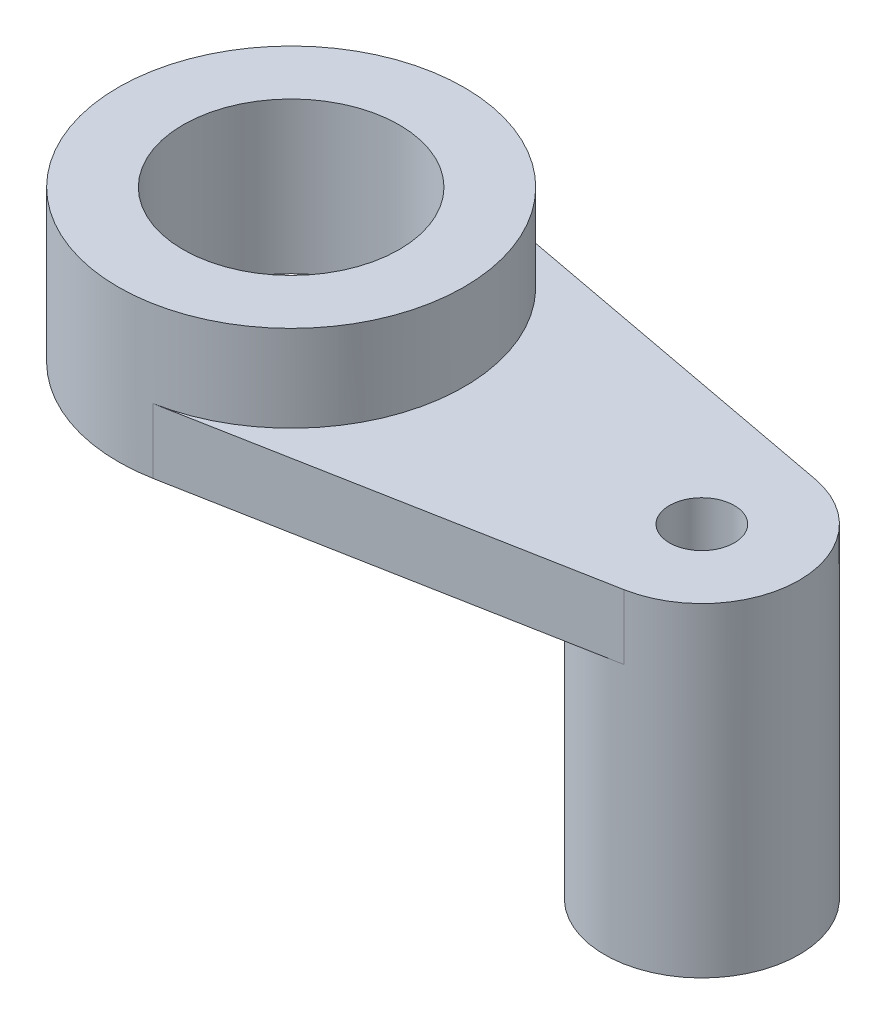
SolidWorks part; units mm, degrees
material "Galvanized Steel"
ref_plane "Front Plane" through (0, 0, 0) normal (0, 0, 1) x (1, 0, 0)
ref_plane "Top Plane" through (0, 0, 0) normal (0, 1, 0) x (1, 0, 0)
ref_plane "Right Plane" through (0, 0, 0) normal (1, 0, 0) x (0, 0, -1)
sketch "Sketch1" plane through (0, 0, 0) normal (0, 1, 0) x (1, 0, 0)
  line L0 (0, 0) -> (30821.0122, 0) construction
  line L1 (0, 0) -> (0, 30821.0122) construction
  line L2 (42.5, 0) -> (42.5, 50000) construction
  circle A0 centre (0, 0) radius 10
  circle A1 centre (0, 0) radius 16
  dimension "D1" = 20
  dimension "D2" = 6
extrude "Boss-Extrude1" add sketch "Sketch1" along normal blind 14
sketch "Sketch2" plane through (0, 0, 0) normal (0, 1, 0) x (1, 0, 0)
  line L0 (38, 0) -> (38, 50000) construction
  line L1 (47, 0.7036) -> (47, 50000.7036) construction
  line L2 (0, 0) -> (50000, 0) construction
  line L3 (2.9474, 15.7262) -> (39.6579, 8.846)
  line L4 (2.9474, -15.7262) -> (39.6579, -8.846)
  arc A1 (39.6579, -8.846) -> (39.6579, 8.846) centre (38, 0) ccw
  arc A2 (2.9474, -15.7262) -> (2.9474, 15.7262) centre (0, 0) ccw
  circle A3 centre (0, 0) radius 16 construction
  dimension "D3" = 38
  dimension "D1" = 38
  dimension "D2" = 9
extrude "Boss-Extrude2" add sketch "Sketch2" along normal blind 6
sketch "Sketch3" plane through (0, 6, 0) normal (0, 1, 0) x (1, 0, 0)
  circle A0 centre (38, 0) radius 3
  point P2 (0, 0)
  dimension "D2" = 6
  dimension "D1" = 38
sketch "Sketch4" plane through (0, 0, 0) normal (0, -1, 0) x (1, 0, 0)
  circle A0 centre (38, 0) radius 9
  dimension "D1" = 18
extrude "Boss-Extrude3" add sketch "Sketch4" along normal blind 24
sketch "Sketch5" plane through (0, 6, 0) normal (0, 1, 0) x (1, 0, 0)
  circle A0 centre (38, 0) radius 3
  dimension "D2" = 6
  dimension "D1" = 38
extrude "Cut-Extrude2" cut sketch "Sketch5" against normal through all both and the other way through all
